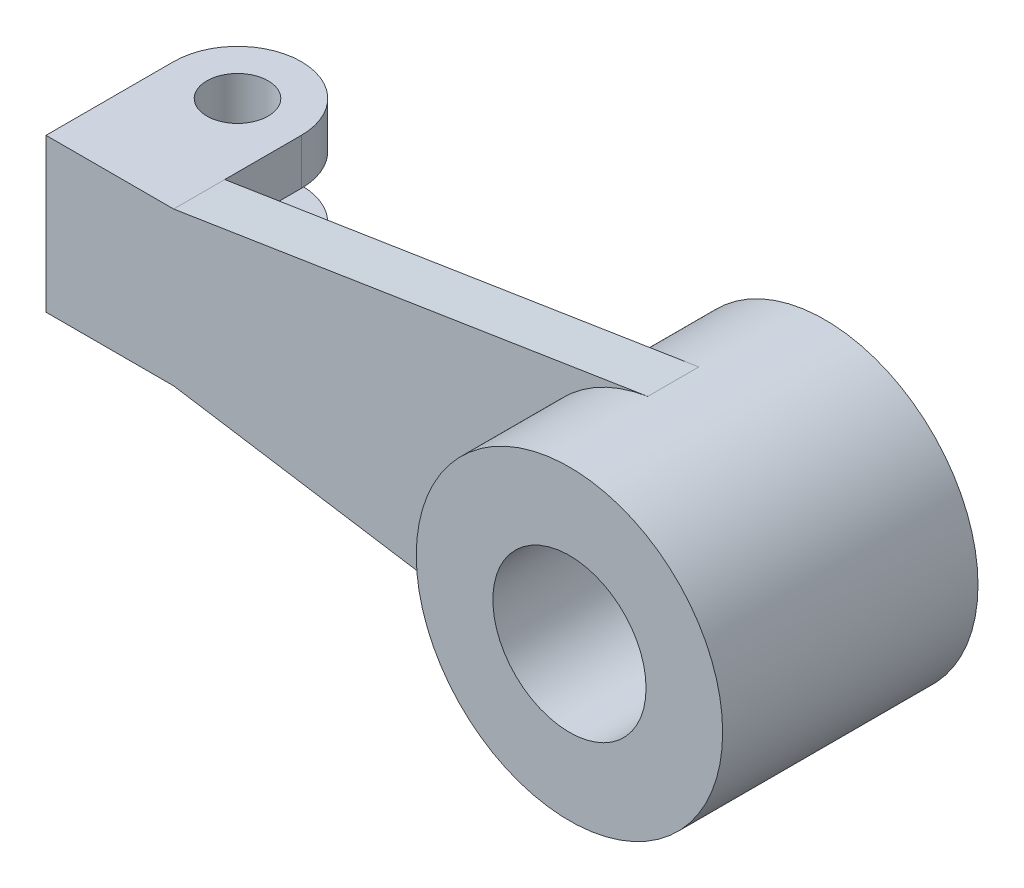
SolidWorks part; units mm, degrees
ref_plane "Front Plane" through (0, 0, 0) normal (0, 0, 1) x (1, 0, 0)
ref_plane "Top Plane" through (0, 0, 0) normal (0, 1, 0) x (1, 0, 0)
ref_plane "Right Plane" through (0, 0, 0) normal (1, 0, 0) x (0, 0, -1)
sketch "Sketch1" plane through (0, 0, 0) normal (0, 0, 1) x (1, 0, 0)
  circle A0 centre (0, 0) radius 30
  circle A1 centre (0, 0) radius 15
  dimension "D1" = 60
  dimension "D2" = 30
extrude "Boss-Extrude1" add sketch "Sketch1" along normal mid plane 50
sketch "Sketch2" plane through (0, 0, 0) normal (0, 0, 1) x (1, 0, 0)
  line L0 (-4.6717, 29.634) -> (-97.5, 15)
  line L1 (-97.5, 15) -> (-122.5, 15)
  line L2 (-122.5, 15) -> (-122.5, -15)
  line L3 (-128.6408, 0) -> (89.5656, 0) construction
  line L4 (-97.5, -15) -> (-122.5, -15)
  line L5 (-4.6717, -29.634) -> (-97.5, -15)
  circle A0 centre (0, 0) radius 30 construction
  arc A1 (-4.6717, 29.634) -> (-4.6717, -29.634) centre (0, 0) ccw
  circle A2 centre (0, 0) radius 30 construction
  point P11 (-122.5, 0)
  dimension "D1" = 30
  dimension "D2" = 25
  dimension "D3" = 122.5
extrude "Boss-Extrude2" add sketch "Sketch2" along normal mid plane 10
sketch "Sketch3" plane through (0, 15, 0) normal (0, 1, 0) x (1, 0, 0)
  line L0 (-97.5, 5) -> (-122.5, 5) construction
  line L1 (-97.5, 5) -> (-122.5, 5)
  line L2 (-122.5, 5) -> (-122.5, 20)
  line L3 (-97.5, -5) -> (-122.5, -5) construction
  line L4 (-97.5, 20) -> (-97.5, 5)
  arc A0 (-97.5, 20) -> (-122.5, 20) centre (-110, 20) ccw
  circle A1 centre (-110, 20) radius 6
  dimension "D2" = 12
  dimension "D1" = 25
extrude "Boss-Extrude3" add sketch "Sketch3" against normal blind 9
mirror "Mirror1" about plane through (0, 0, 0) normal (0, 1, 0) of "Boss-Extrude2", "Boss-Extrude3"
